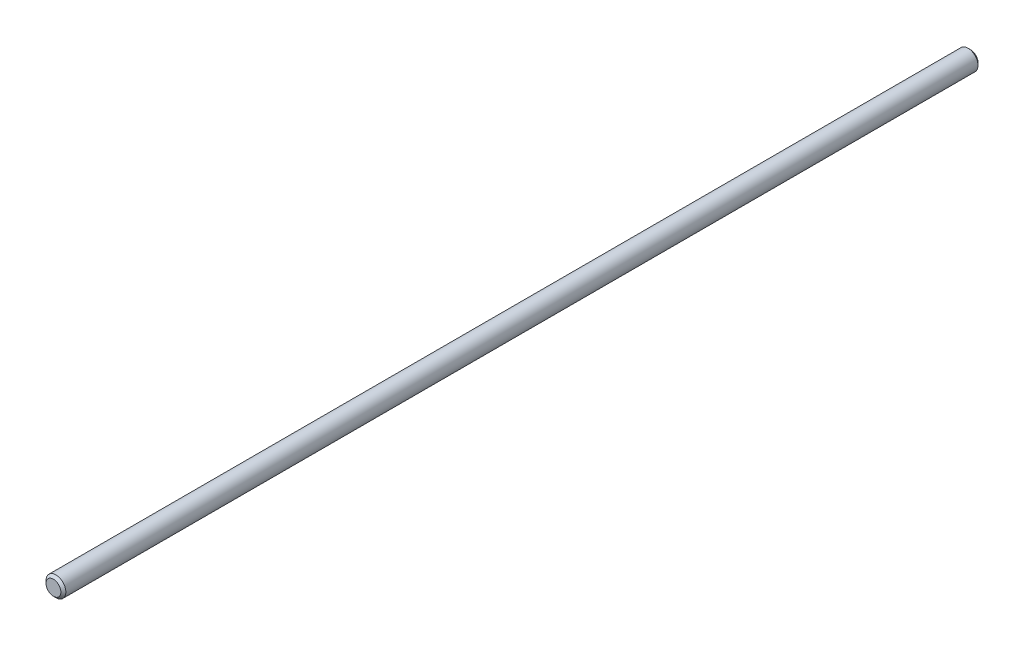
SolidWorks part; units mm, degrees
ref_plane "Piano frontale" through (0, 0, 0) normal (0, 0, 1) x (1, 0, 0)
ref_plane "Piano superiore" through (0, 0, 0) normal (0, 1, 0) x (1, 0, 0)
ref_plane "Piano destro" through (0, 0, 0) normal (1, 0, 0) x (0, 0, -1)
sketch "Schizzo1" plane through (0, 0, 0) normal (0, 0, 1) x (1, 0, 0)
  circle A0 centre (0, 0) radius 4
  dimension "D1" = 8
extrude "Estrusione-Estrusione1" add sketch "Schizzo1" along normal blind 370
chamfer "Smusso1" distance 1 angle 45 2 edges at (4, 0, 0) (4, 0, 370)
sketch "Schizzo2" plane through (0, 0, 0) normal (0, 1, 0) x (1, 0, 0)
  line L0 (4, -1) -> (4, -369) construction
